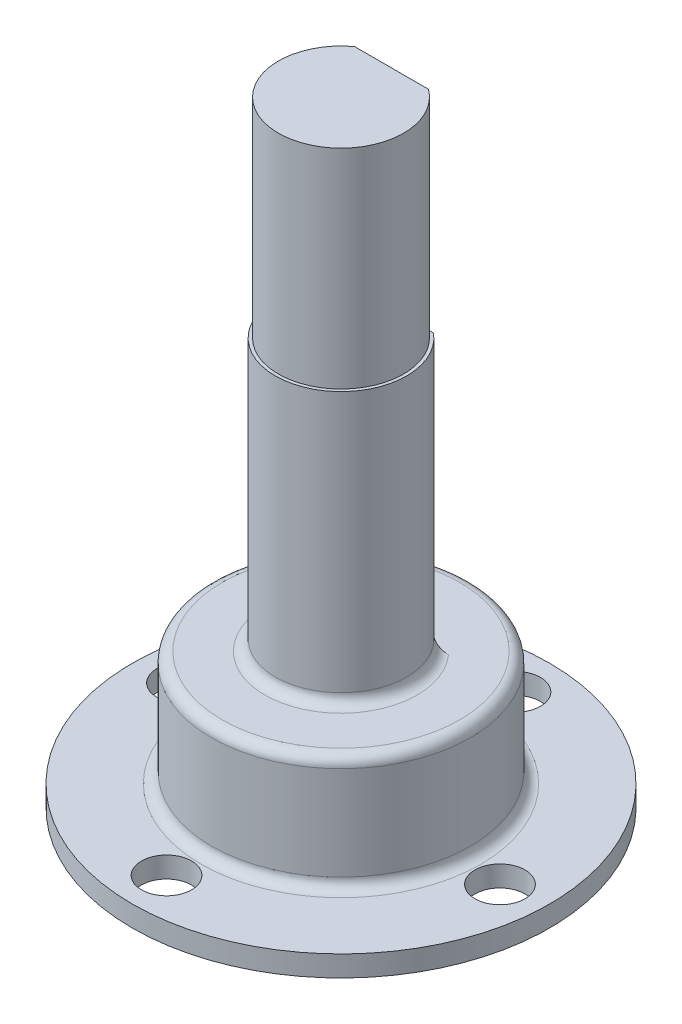
SolidWorks part; units mm, degrees
material "ABS"
ref_plane "Plan de face" through (0, 0, 0) normal (0, 0, 1) x (1, 0, 0)
ref_plane "Plan de dessus" through (0, 0, 0) normal (0, 1, 0) x (1, 0, 0)
ref_plane "Plan de droite" through (0, 0, 0) normal (1, 0, 0) x (0, 0, -1)
sketch "Esquisse2" plane through (0, 0, 0) normal (0, 0, 1) x (1, 0, 0)
  line L0 (0, 29.5) -> (3, 29.5)
  line L3 (6.2, 3) -> (6.2, 1)
  line L4 (6.2, 1) -> (10, 1)
  line L5 (10, 1) -> (10, 0)
  line L6 (10, 0) -> (4.5, 0)
  line L7 (4.5, 0) -> (4.5, 3)
  line L8 (4.5, 3) -> (0, 3)
  line L9 (0, 3) -> (0, 29.5)
  line L11 (3.15, 19.5) -> (3.15, 6.5)
  line L12 (3.15, 6.5) -> (6.2, 6.5)
  line L13 (6.2, 3) -> (6.2, 6.5)
  line L14 (3, 29.5) -> (3, 19.5)
  line L15 (3, 19.5) -> (3.15, 19.5)
  point P2 (1.5, 29.5)
  dimension "D1" = 10
  dimension "D2" = 29.5
  dimension "D3" = 0
  dimension "D4" = 1
  dimension "D5" = 4.5
  dimension "D6" = 2
  dimension "D7" = 6.5
  dimension "D8" = 3
  dimension "D9" = 3.15
  dimension "D10" = 0
  dimension "D11" = 3
  dimension "D12" = 1.7
  dimension "D13" = 10
revolve "Révolution2" add sketch "Esquisse2" angle 360 about L9
sketch "Esquisse3" plane through (0, 29.5, 0) normal (0, 1, 0) x (1, 0, 0)
  line L1 (-3.6413, 2.4219) -> (2.9365, 2.4219)
  line L2 (-3.6413, 2.4219) -> (-3.6413, 3.808)
  line L3 (-3.6413, 3.808) -> (2.9365, 3.808)
  line L4 (2.9365, 2.4219) -> (2.9365, 3.808)
  dimension "D1" = 6.5779
extrude "Enlèv. mat.-Extru.1" cut sketch "Esquisse3" against normal up to surface (23 mm away) contours L4 L3 L2 L1 up to face at (0, 6.5, -3.15)
hole_wizard "Dégagement M21" positions "Esquisse4" profile "Esquisse5" hole size "M2" standard "Ansi Metric" end condition up to next
sketch "Esquisse4" plane through (0, 1, 0) normal (0, 1, 0) x (1, 0, 0)
  circle A0 centre (0, 0) radius 8 construction
  point P0 (0.3713, 7.9914)
  dimension "D1" = 16
sketch "Esquisse5" plane through (0.3713, 1, -7.9914) normal (1, 0, 0) x (0, 0, 1)
  line L0 (0, 0) -> (0, 1.001)
  line L1 (0, 1.001) -> (1.2, 1.001)
  line L2 (1.2, 1.001) -> (1.2, 0)
  line L5 (1.2, 0) -> (0, 0)
  line L11 (0, -6.35) -> (0, 107.95) construction
  dimension "Diamètre du perçage jusqu'au prochain" = 2.4
  dimension "Profondeur du perçage jusqu'au prochain" = 1.001
pattern_circular "Répétition circulaire1" count 4 over 360 about axis through (0, 0, 0) along (0, 1, 0) of "Dégagement M21"
fillet "Fillet1" radius 0.5 3 edges at (0, 1, -6.2) (0, 6.5, -6.2) (0, 6.5, 3.15)
